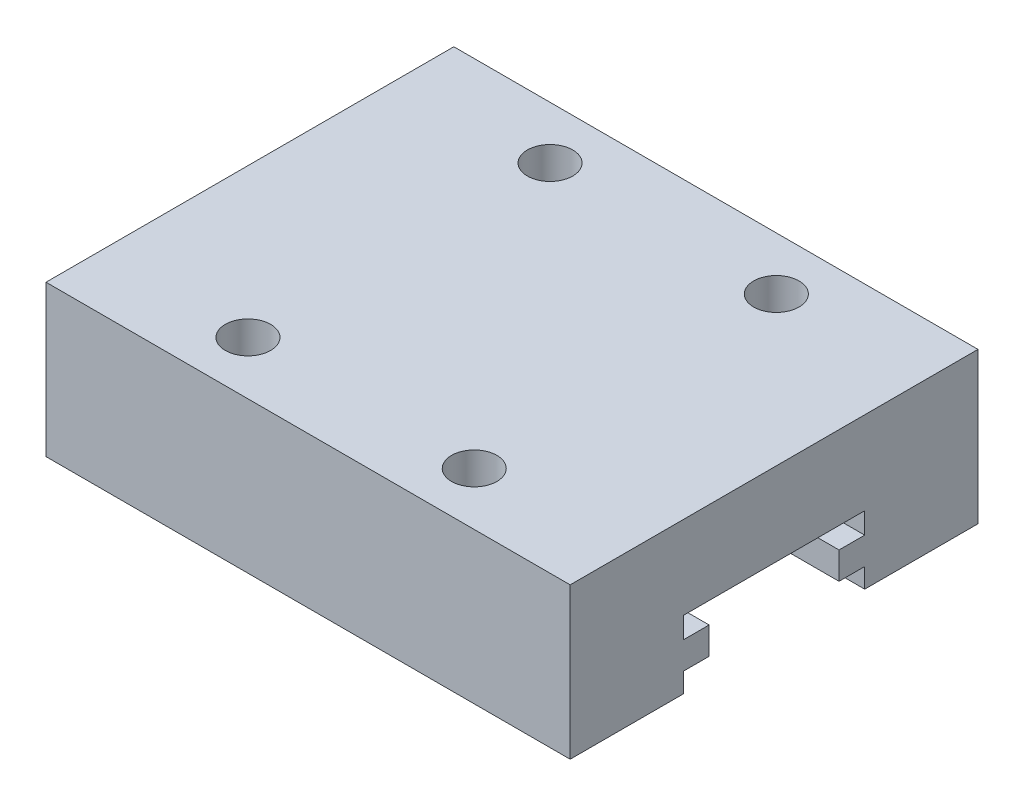
SolidWorks part; units mm, degrees
ref_plane "Alzado" through (0, 0, 0) normal (0, 0, 1) x (1, 0, 0)
ref_plane "Planta" through (0, 0, 0) normal (0, 1, 0) x (1, 0, 0)
ref_plane "Vista lateral" through (0, 0, 0) normal (1, 0, 0) x (0, 0, -1)
sketch "Croquis1" plane through (0, 0, 0) normal (0, 1, 0) x (1, 0, 0)
  line L2 (0, 0) -> (34.7, 0)
  line L3 (0, 0) -> (0, 27)
  line L4 (0, 27) -> (34.7, 27)
  line L5 (34.7, 0) -> (34.7, 27)
  dimension "D1" = 34.7
  dimension "D2" = 27
extrude "Saliente-Extruir1" add sketch "Croquis1" along normal blind 10
sketch "Croquis2" plane through (0, 10, 0) normal (0, 1, 0) x (1, 0, 0)
  line L0 (0, 0) -> (34.7, 0) construction
  line L2 (17.35, 0) -> (17.35, 27) construction
  line L3 (34.7, 27) -> (0, 27) construction
  circle A0 centre (9.85, 23.5201) radius 1.5
  circle A1 centre (24.85, 23.5) radius 1.5
  circle A2 centre (9.85, 3.5201) radius 1.5
  circle A3 centre (24.85, 3.5) radius 1.5
  dimension "D1" = 3
  dimension "D2" = 15
  dimension "D3" = 15
  dimension "D4" = 20
  dimension "D5" = 20
  dimension "D6" = 3.5
  dimension "D7" = 7.5
  dimension "D8" = 15
  dimension "D9" = 7.5
extrude "Cortar-Extruir1" cut sketch "Croquis2" against normal blind 5
sketch "Croquis3" plane through (34.7, 0, 0) normal (1, 0, 0) x (0, 0, -1)
  line L0 (0, 0) -> (27, 0) construction
  line L1 (7.5, 0) -> (19.5, 0)
  line L2 (7.5, 0) -> (7.5, 1.3)
  line L3 (7.5, 4.5) -> (19.5, 4.5)
  line L4 (19.5, 0) -> (19.5, 1.3)
  line L5 (13.5, 10) -> (13.5, 0) construction
  line L6 (0, 10) -> (27, 10) construction
  line L7 (7.5, 3.1) -> (7.5, 4.5)
  line L8 (7.5, 3.1) -> (9.2, 3.1)
  line L10 (7.5, 1.3) -> (9.2, 1.3)
  line L11 (9.2, 3.1) -> (9.2, 1.3)
  line L12 (19.5, 1.3) -> (17.8, 1.3)
  line L13 (19.5, 3.1) -> (17.8, 3.1)
  line L14 (17.8, 3.1) -> (17.8, 1.3)
  line L15 (19.5, 3.1) -> (19.5, 4.5)
  dimension "D2" = 4.5
  dimension "D3" = 6
  dimension "D4" = 1.8
  dimension "D5" = 1.7
  dimension "D6" = 1.4
extrude "Cortar-Extruir2" cut sketch "Croquis3" against normal up to surface (34.7 mm away) up to face at (0, 5, -13.5)
